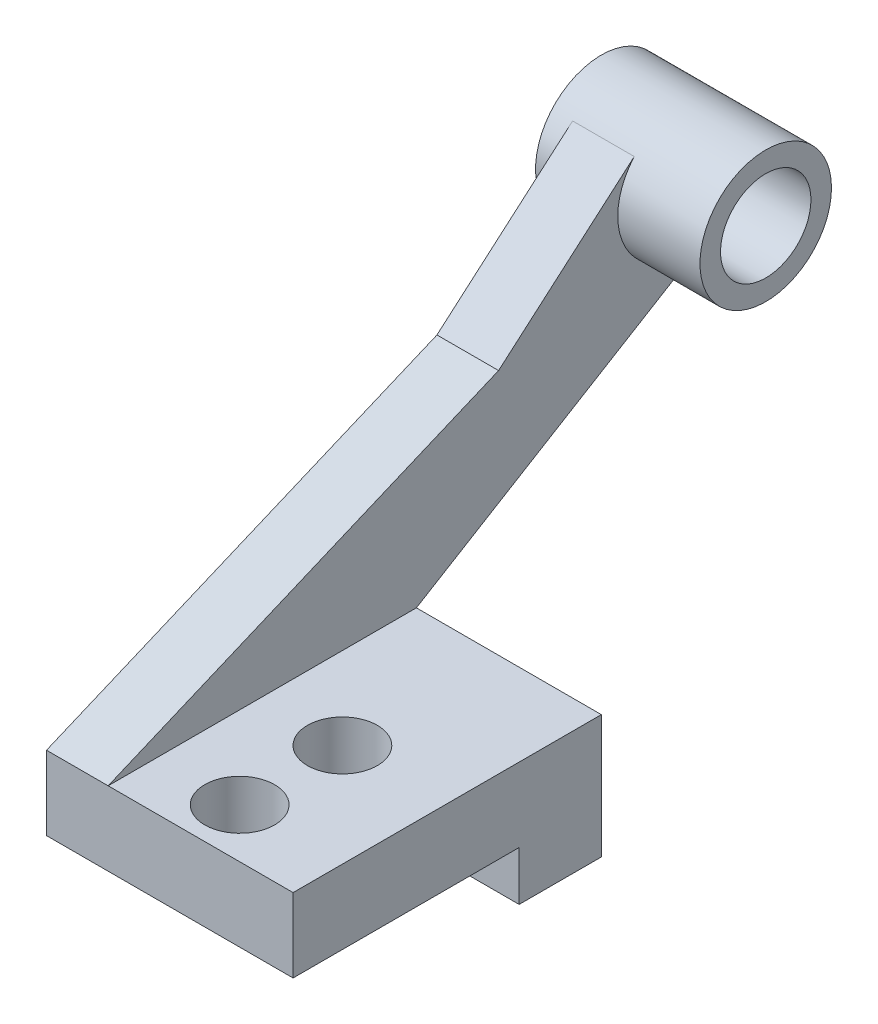
SolidWorks part; units mm, degrees
ref_plane "Front Plane" through (0, 0, 0) normal (0, 0, 1) x (1, 0, 0)
ref_plane "Top Plane" through (0, 0, 0) normal (0, 1, 0) x (1, 0, 0)
ref_plane "Right Plane" through (0, 0, 0) normal (1, 0, 0) x (0, 0, -1)
sketch "Sketch1" plane through (0, 0, 0) normal (1, 0, 0) x (0, 0, -1)
  line L0 (-31.5706, -10.4434) -> (-31.5706, -28.4434)
  line L1 (-31.5706, -10.4434) -> (43.4294, -10.4434)
  line L2 (43.4294, -10.4434) -> (43.4294, -40.4434)
  line L3 (43.4294, -40.4434) -> (23.4294, -40.4434)
  line L4 (23.4294, -40.4434) -> (23.4294, -28.4434)
  line L5 (23.4294, -28.4434) -> (-31.5706, -28.4434)
extrude "Boss-Extrude1" add sketch "Sketch1" along normal blind 60
sketch "Sketch2" plane through (0, -10.4434, 0) normal (0, 1, 0) x (1, 0, 0)
  line L0 (60, -31.5706) -> (60, -19.5706) construction
  line L1 (60, 43.4294) -> (60, -31.5706) construction
  circle A0 centre (35, -19.5706) radius 8.5
  circle A1 centre (35, 5.4294) radius 8.5
extrude "Cut-Extrude1" cut sketch "Sketch2" against normal blind 60 contours A0 | A1
sketch3d "3DSketch1"
  line L0 (0, -10.4434, 31.5706) -> (0, -10.4434, -43.4294)
  line L7 (0, -10.4434, 31.5706) -> (0, 29.5566, 31.5706) construction
  line L8 (0, 29.5566, 31.5706) -> (0, 29.5566, -63.4294) construction
  line L9 (0, -10.4434, 31.5706) -> (0, 29.5566, -63.4294)
  line L17 (0, -10.4434, -43.4294) -> (0, -10.4434, -108.4294) construction
  line L18 (0, 47.5566, -108.4294) -> (0, -10.4434, -108.4294) construction
  line L21 (0, -10.4434, -43.4294) -> (0, 34.1763, -117.2024) construction
  line L22 (0, -10.4434, -43.4294) -> (0, 34.1763, -117.2024)
  line L24 (0, 29.5566, -63.4294) -> (0, 60.937, -99.6563) construction
  line L25 (0, 34.1763, -117.2024) -> (0, 60.937, -99.6563)
  line L26 (0, 29.5566, -63.4294) -> (0, 60.937, -99.6563)
extrude "Boss-Extrude2" add sketch "3DSketch1" along direction (1, 0, 0) on the side of the normal blind 15
sketch "Sketch3" plane through (15, 0, 0) normal (1, 0, 0) x (0, 0, -1)
  line L0 (99.6563, 60.937) -> (117.2024, 34.1763) construction
  circle A0 centre (108.4294, 47.5566) radius 16
  circle A1 centre (108.4294, 47.5566) radius 11
extrude "Boss-Extrude3" add sketch "Sketch3" against normal blind 20 and the other way blind 20
sketch "Sketch4" plane through (15, 0, 0) normal (1, 0, 0) x (0, 0, -1)
  line L0 (102.3979, 56.7556) -> (114.4608, 38.3577)
  line L1 (114.4608, 38.3577) -> (102.3979, 56.7556)
  arc A0 (114.4608, 38.3577) -> (102.3979, 56.7556) centre (108.4294, 47.5566) cw
  arc M1 (102.3979, 56.7556) -> (114.4608, 38.3577) centre (108.4294, 47.5566) ccw
  line M2 (114.4608, 38.3577) -> (102.3979, 56.7556)
extrude "Cut-Extrude2" cut sketch "Sketch4" against normal blind 57 contours M2 M1
